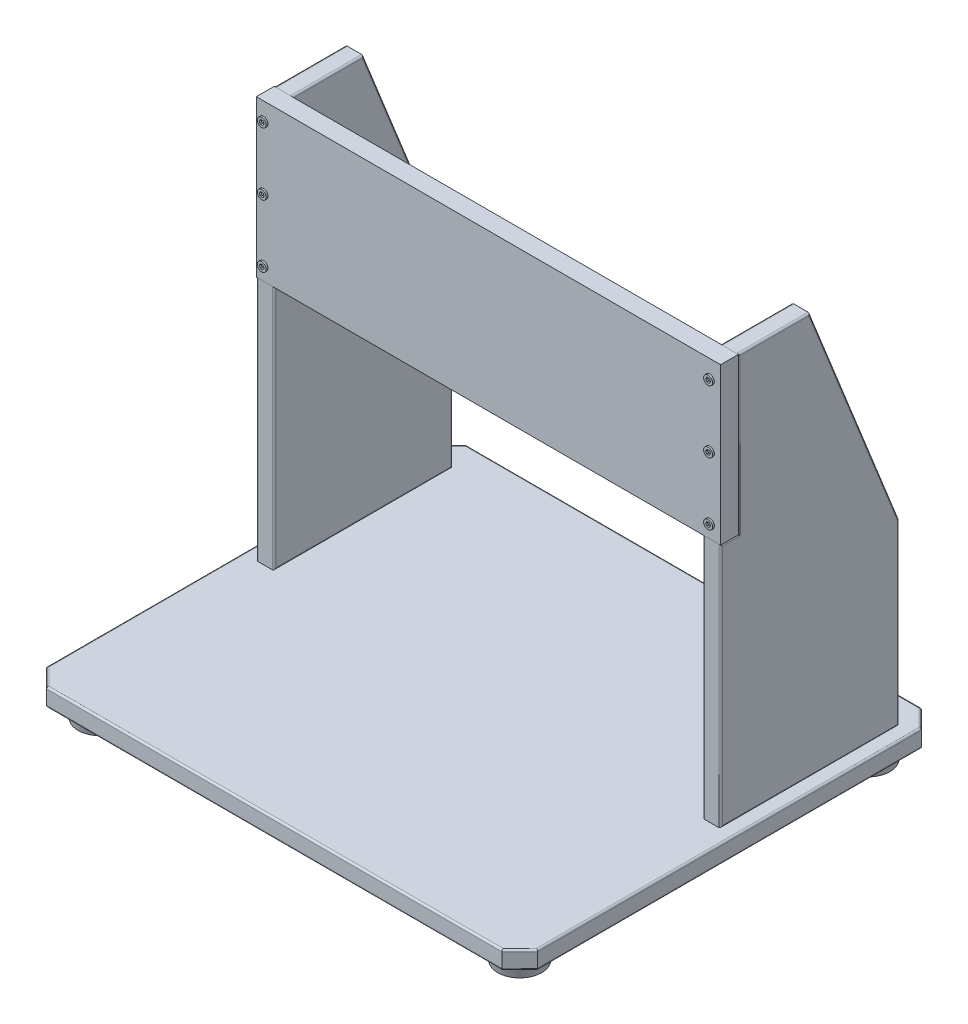
SolidWorks part; units mm, degrees
ref_plane "Front Plane" through (0, 0, 0) normal (0, 0, 1) x (1, 0, 0)
ref_plane "Top Plane" through (0, 0, 0) normal (0, 1, 0) x (1, 0, 0)
ref_plane "Right Plane" through (0, 0, 0) normal (1, 0, 0) x (0, 0, -1)
sketch "Sketch1" plane through (0, 0, 0) normal (0, 1, 0) x (1, 0, 0)
  line L1 (-275, 235) -> (275, 235)
  line L2 (-275, 235) -> (-275, -235)
  line L3 (-275, -235) -> (275, -235)
  line L4 (275, 235) -> (275, -235)
  line L5 (-275, 235) -> (275, -235) construction
  line L6 (-275, -235) -> (275, 235) construction
  point P0 (0, 0)
  dimension "D1" = 550
  dimension "D2" = 470
extrude "Boss-Extrude1" add sketch "Sketch1" along normal blind 20
chamfer "Chamfer1" distance 20 angle 45 4 edges at (275, 10, -235) (-275, 10, -235) (275, 10, 235) (-275, 10, 235)
sketch "Sketch2" plane through (0, 20, 0) normal (0, 1, 0) x (1, 0, 0)
  line L0 (0, 0) -> (0, 235) construction
  line L1 (255, 235) -> (-255, 235) construction
  line L2 (-275, 215) -> (-275, -215) construction
  line L3 (-260, 205) -> (-240, 205)
  line L4 (-260, 205) -> (-260, 5)
  line L5 (-260, 5) -> (-240, 5)
  line L6 (-240, 205) -> (-240, 5)
  dimension "D1" = 20
  dimension "D2" = 200
  dimension "D3" = 30
  dimension "D4" = 15
extrude "Boss-Extrude2" add sketch "Sketch2" along normal blind 450 separate body
sketch "Sketch3" plane through (-260, 0, 0) normal (-1, 0, 0) x (0, 0, 1)
  line L0 (-205, 220) -> (-105, 470)
  line L1 (-205, 470) -> (-205, 20) construction
  line L2 (-205, 470) -> (-5, 470) construction
  line L3 (-25, 470) -> (-25, 295)
  line L4 (-25, 295) -> (-5, 295)
  line L5 (-5, 470) -> (-5, 20) construction
  line M4 (-5, 20) -> (-5, 470)
  line M5 (-5, 470) -> (-205, 470)
  line M6 (-205, 470) -> (-205, 20)
  dimension "D1" = 100
  dimension "D2" = 250
  dimension "D3" = 20
  dimension "D4" = 175
extrude "Cut-Extrude1" cut sketch "Sketch3" against normal blind 515 contours L0 M6 M5 | L3 L4 M4 M5
mirror "Mirror1" about plane through (0, 0, 0) normal (1, 0, 0) of bodies 103
sketch "Sketch4" plane through (0, 0, -25) normal (0, 0, 1) x (1, 0, 0)
  line L1 (-260, 470) -> (260, 470)
  line L2 (-260, 470) -> (-260, 295)
  line L3 (-260, 295) -> (260, 295)
  line L4 (260, 470) -> (260, 295)
extrude "Boss-Extrude3" add sketch "Sketch4" along normal blind 20 separate body
sketch "Sketch5" plane through (0, 0, 0) normal (0, -1, 0) x (1, 0, 0)
  line L0 (-275, -215) -> (-275, 215) construction
  line L2 (-255, 235) -> (255, 235) construction
  circle A0 centre (-235, 195) radius 30
  dimension "D1" = 60
  dimension "D2" = 40
  dimension "40" = 40
extrude "Boss-Extrude4" add sketch "Sketch5" along normal blind 20 draft 15 separate body
mirror "Mirror2" about plane through (0, 0, 0) normal (1, 0, 0) of bodies 106
mirror "Mirror3" about plane through (0, 0, 0) normal (0, 0, 1) of bodies 106 107
fillet "Fillet1" radius 2 16 edges at (-265, 0, -225) (-275, 0, 0) (-265, 0, 225) (0, 0, 235) (265, 0, 225) (275, 0, 0) (265, 0, -225) (0, 0, -235) (265, 20, 225) (0, 20, 235) (-265, 20, 225) (-275, 20, 0) (-265, 20, -225) (0, 20, -235) (265, 20, -225) (275, 20, 0)
fillet "Fillet2" radius 2 14 edges at (-240, 20, -105) (-240, 157.5, -5) (-240, 295, -15) (-240, 382.5, -25) (-240, 470, -65) (-240, 345, -155) (-240, 120, -205) (-260, 382.5, -25) (-260, 295, -15) (-260, 157.5, -5) (-260, 20, -105) (-260, 120, -205) (-260, 345, -155) (-260, 470, -65)
fillet "Fillet3" radius 2 14 edges at (260, 345, -155) (260, 120, -205) (260, 20, -105) (260, 157.5, -5) (260, 295, -15) (260, 382.5, -25) (260, 470, -65) (240, 345, -155) (240, 470, -65) (240, 382.5, -25) (240, 295, -15) (240, 157.5, -5) (240, 20, -105) (240, 120, -205)
sketch "Sketch6" plane through (0, 0, -5) normal (0, 0, 1) x (1, 0, 0)
  line L0 (-260, 470) -> (-260, 295) construction
  line L1 (260, 470) -> (-260, 470) construction
  line L3 (-249.2305, 450) -> (-250.6152, 452.3985)
  line L4 (-250.6152, 452.3985) -> (-253.3848, 452.3985)
  line L5 (-253.3848, 452.3985) -> (-254.7695, 450)
  line L6 (-254.7695, 450) -> (-253.3848, 447.6015)
  line L7 (-253.3848, 447.6015) -> (-250.6152, 447.6015)
  line L8 (-250.6152, 447.6015) -> (-249.2305, 450)
  circle A0 centre (-252, 450) radius 5
  circle A1 centre (-252, 450) radius 2.3985 construction
  point P6 (-249.2305, 450)
  dimension "D1" = 10
  dimension "D2" = 8
  dimension "D3" = 20
extrude "Boss-Extrude5" add sketch "Sketch6" along normal blind 2 separate body
pattern_linear "LPattern3" count 2 spacing 500 along (1, 0, 0) count 3 spacing 70 along (0, -1, 0) of bodies 110
